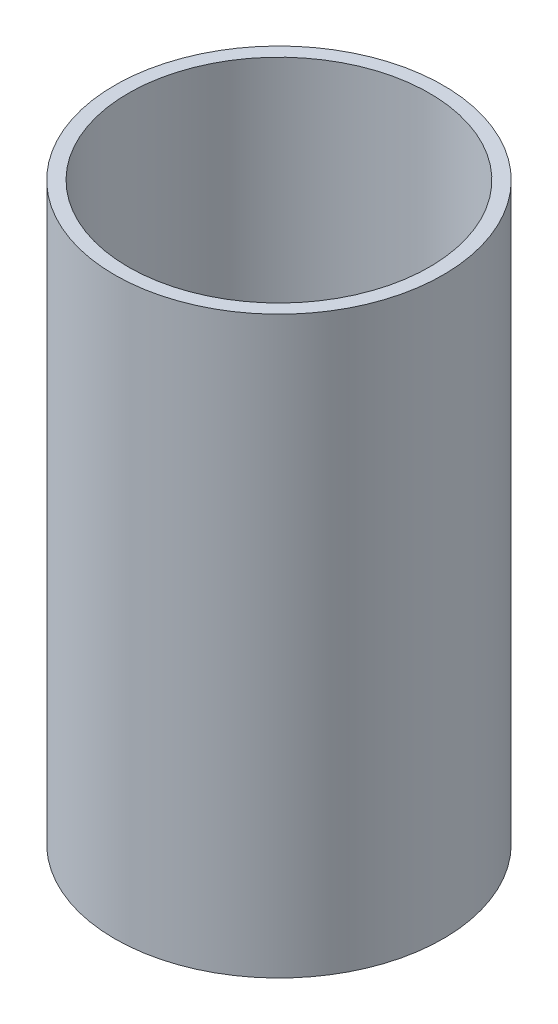
SolidWorks part; units mm, degrees
ref_plane "Front Plane" through (0, 0, 0) normal (0, 0, 1) x (1, 0, 0)
ref_plane "Top Plane" through (0, 0, 0) normal (0, 1, 0) x (1, 0, 0)
ref_plane "Right Plane" through (0, 0, 0) normal (1, 0, 0) x (0, 0, -1)
sketch "Sketch1" plane through (0, 0, 0) normal (0, 1, 0) x (1, 0, 0)
  circle A0 centre (0, 0) radius 12
  circle A1 centre (0, 0) radius 11
  dimension "D1" = 24
  dimension "D2" = 22
extrude "Boss-Extrude1" add sketch "Sketch1" along normal mid plane 42
